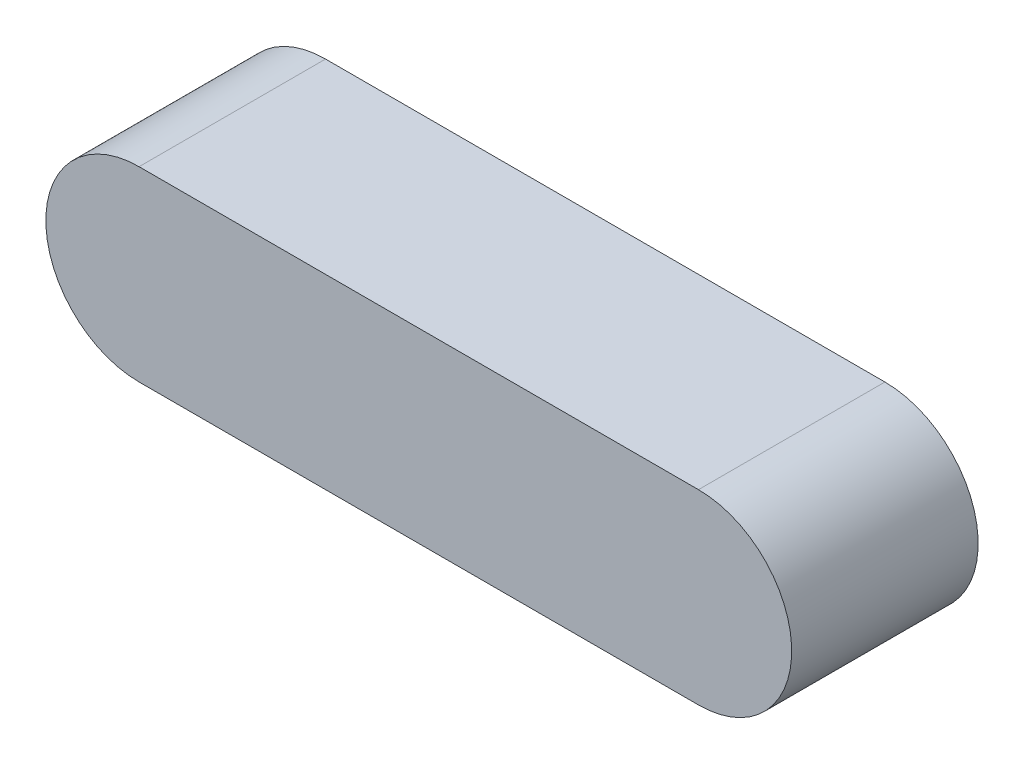
SolidWorks part; units mm, degrees
ref_plane "Front Plane" through (0, 0, 0) normal (0, 0, 1) x (1, 0, 0)
ref_plane "Top Plane" through (0, 0, 0) normal (0, 1, 0) x (1, 0, 0)
ref_plane "Right Plane" through (0, 0, 0) normal (1, 0, 0) x (0, 0, -1)
sketch "Sketch1" plane through (0, 0, 0) normal (0, 1, 0) x (1, 0, 0)
  line L0 (-6.35, 0) -> (6.35, 0) construction
  line L1 (-6.35, 1.5875) -> (6.35, 1.5875)
  line L2 (-6.35, 1.5875) -> (-6.35, -1.5875)
  line L3 (-6.35, -1.5875) -> (6.35, -1.5875)
  line L4 (6.35, 1.5875) -> (6.35, -1.5875)
  dimension "Square Size" = 3.175
  dimension "Length" = 12.7
extrude "Extrude1" add sketch "Sketch1" against normal blind 3.175
sketch "Sketch2" plane through (44.45, 6.35, 1.5875) normal (0, 0, -1) x (-1, 0, 0)
  line L0 (39.6875, -7.9375) -> (49.2125, -7.9375) construction
  line L1 (39.6875, -6.35) -> (49.2125, -6.35)
  line L2 (39.6875, -9.525) -> (49.2125, -9.525)
  line L5 (50.8, -7.9375) -> (49.2125, -7.9375) construction
  line L6 (39.6875, -7.9375) -> (38.1, -7.9375) construction
  line L7 (38.1, -9.525) -> (38.1, -6.35) construction
  line L8 (50.8, -9.525) -> (50.8, -6.35) construction
  line L9 (38.1, -6.35) -> (50.8, -6.35) construction
  arc A0 (39.6875, -6.35) -> (39.6875, -9.525) centre (39.6875, -7.9375) ccw
  arc A1 (49.2125, -9.525) -> (49.2125, -6.35) centre (49.2125, -7.9375) ccw
  point P2 (44.45, -7.9375)
  dimension "D1" = 9.525
  dimension "D2" = 1.5875
  dimension "D3" = 1.5875
  dimension "D4" = 1.5875
  dimension "D5" = 1.5875
extrude "Extrude2" cut sketch "Sketch2" along normal through all flip side to cut
sketch "Sketch3" plane through (0, 0, 0) normal (0, 1, 0) x (1, 0, 0)
  line L0 (0, -1.5875) -> (0, 1.5875) construction
  line L1 (-4.7625, -1.5875) -> (4.7625, -1.5875) construction
  line L2 (4.7625, 1.5875) -> (-4.7625, 1.5875) construction
  dimension "D1" = 3.175
